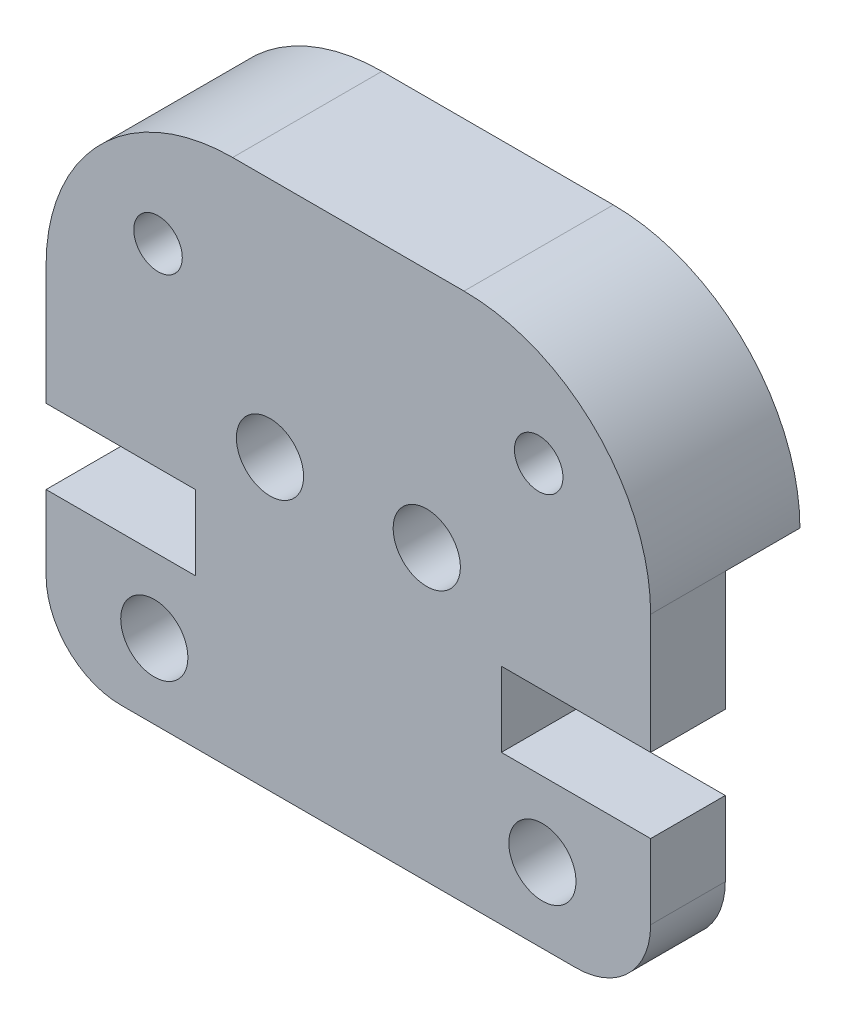
SolidWorks part; units mm, degrees
ref_plane "Front Plane" through (0, 0, 0) normal (0, 0, 1) x (1, 0, 0)
ref_plane "Top Plane" through (0, 0, 0) normal (0, 1, 0) x (1, 0, 0)
ref_plane "Right Plane" through (0, 0, 0) normal (1, 0, 0) x (0, 0, -1)
sketch "Sketch1" plane through (0, 0, 0) normal (0, 0, 1) x (1, 0, 0)
  line L0 (8.1, 14.205) -> (8.1, 0) construction
  line L1 (12.2, 4) -> (16.2, 4)
  line L2 (12.2, 6) -> (12.2, 4)
  line L3 (16.2, 6) -> (12.2, 6)
  line L4 (16.2, 2) -> (16.2, 4)
  line L5 (16.2, 9.205) -> (16.2, 6)
  line L14 (0, 9.205) -> (0, 6)
  line L15 (5, 14.205) -> (11.2, 14.205)
  line L16 (2, 0) -> (14.2, 0)
  line L18 (0, 2) -> (0, 4)
  line L19 (0, 6) -> (4, 6)
  line L21 (4, 6) -> (4, 4)
  line L22 (4, 4) -> (0, 4)
  circle A0 centre (13.3, 2) radius 0.9
  arc A1 (16.2, 2) -> (14.2, 0) centre (14.2, 2) cw
  circle A2 centre (13.2, 11.205) radius 0.65
  arc A3 (11.2, 14.205) -> (16.2, 9.205) centre (11.2, 9.205) cw
  circle A4 centre (10.2, 7.75) radius 0.9
  circle A11 centre (6, 7.75) radius 0.9
  arc A13 (5, 14.205) -> (0, 9.205) centre (5, 9.205) ccw
  circle A15 centre (3, 11.205) radius 0.65
  arc A17 (0, 2) -> (2, 0) centre (2, 2) ccw
  circle A19 centre (2.9, 2) radius 0.9
  dimension "D1" = 1.3
  dimension "D2" = 1.8
  dimension "D3" = 5
  dimension "D4" = 2
  dimension "D5" = 3
  dimension "D6" = 6
  dimension "D7" = 8.1
  dimension "D8" = 7.75
  dimension "D9" = 3
  dimension "D10" = 14.205
extrude "Boss-Extrude1" add sketch "Sketch1" along normal blind 4
sketch "Sketch2" plane through (0, 0, 0) normal (0, 0, -1) x (-1, 0, 0)
  line L0 (0, 0) -> (0, 9.205)
  line L1 (0, 9.205) -> (-16.2, 9.205)
  line L2 (-16.2, 9.205) -> (-16.2, 0)
  line L3 (-16.2, 0) -> (0, 0)
extrude "Cut-Extrude1" cut sketch "Sketch2" against normal blind 2
equation "\"D7@Sketch1\"= \"fingerWidth@parametersSketch@prostheticParameters.SLDPRT\" / 2 'DIP width"
equation "\"D10@Sketch1\"= \"HL@parametersSketch@prostheticParameters.SLDPRT\" * 0.093 - 3 'DIP length - Sil. Sht DIP"
equation "\"D1@Sketch1\"= 1 + \"tol1@parametersSketch@prostheticParameters.SLDPRT\""
equation "\"D2@Sketch1\"= 1.5 + \"tol1@parametersSketch@prostheticParameters.SLDPRT\""
